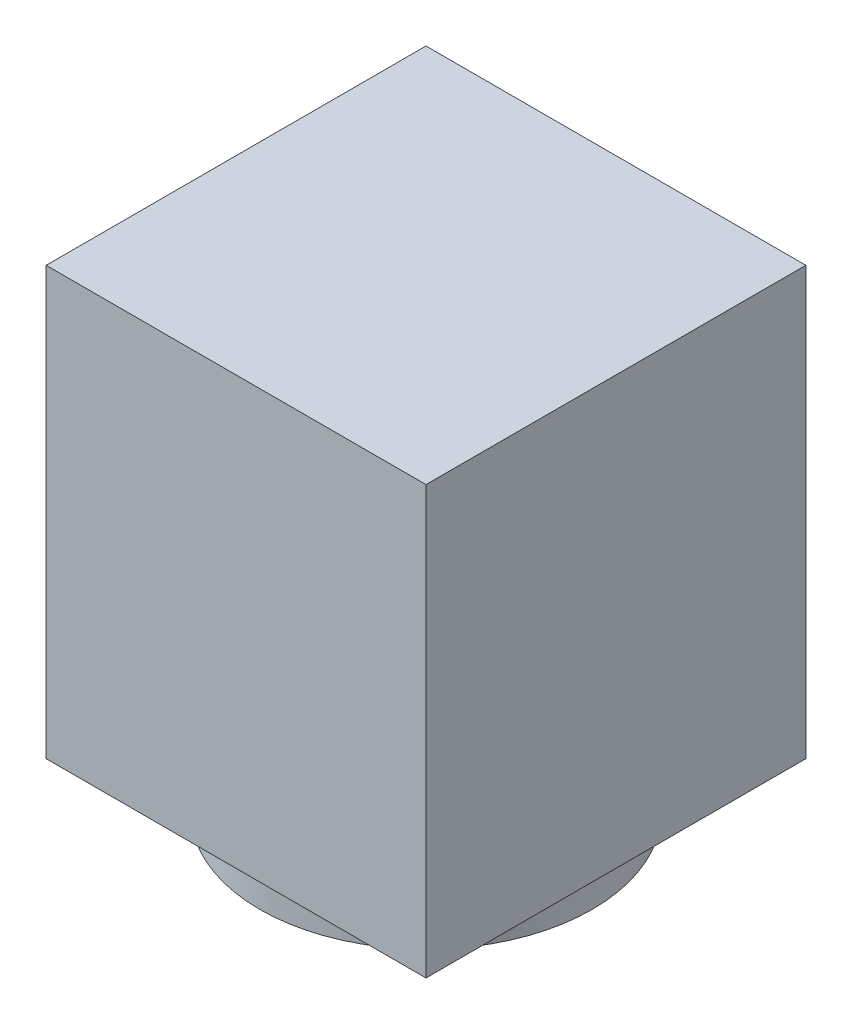
SolidWorks part; units mm, degrees
ref_plane "前视基准面" through (0, 0, 0) normal (0, 0, 1) x (1, 0, 0)
ref_plane "上视基准面" through (0, 0, 0) normal (0, 1, 0) x (1, 0, 0)
ref_plane "右视基准面" through (0, 0, 0) normal (1, 0, 0) x (0, 0, -1)
sketch "草图1" plane through (0, 0, 0) normal (0, 1, 0) x (1, 0, 0)
  circle A0 centre (0, 0) radius 7
extrude "凸台-拉伸1" add sketch "草图1" along normal blind 2
sketch "草图2" plane through (0, 2, 0) normal (0, 1, 0) x (1, 0, 0)
  line L0 (0, 0) -> (10.4307, 0) construction
  line L1 (-8, 8) -> (8, 8)
  line L2 (-8, 8) -> (-8, -8)
  line L3 (-8, -8) -> (8, -8)
  line L4 (8, 8) -> (8, -8)
  line L5 (0, 0) -> (0, -9.7125) construction
  dimension "D1" = 16
  dimension "D2" = 8
  dimension "D3" = 16
  dimension "D4" = 8
extrude "凸台-拉伸2" add sketch "草图2" along normal blind 18
